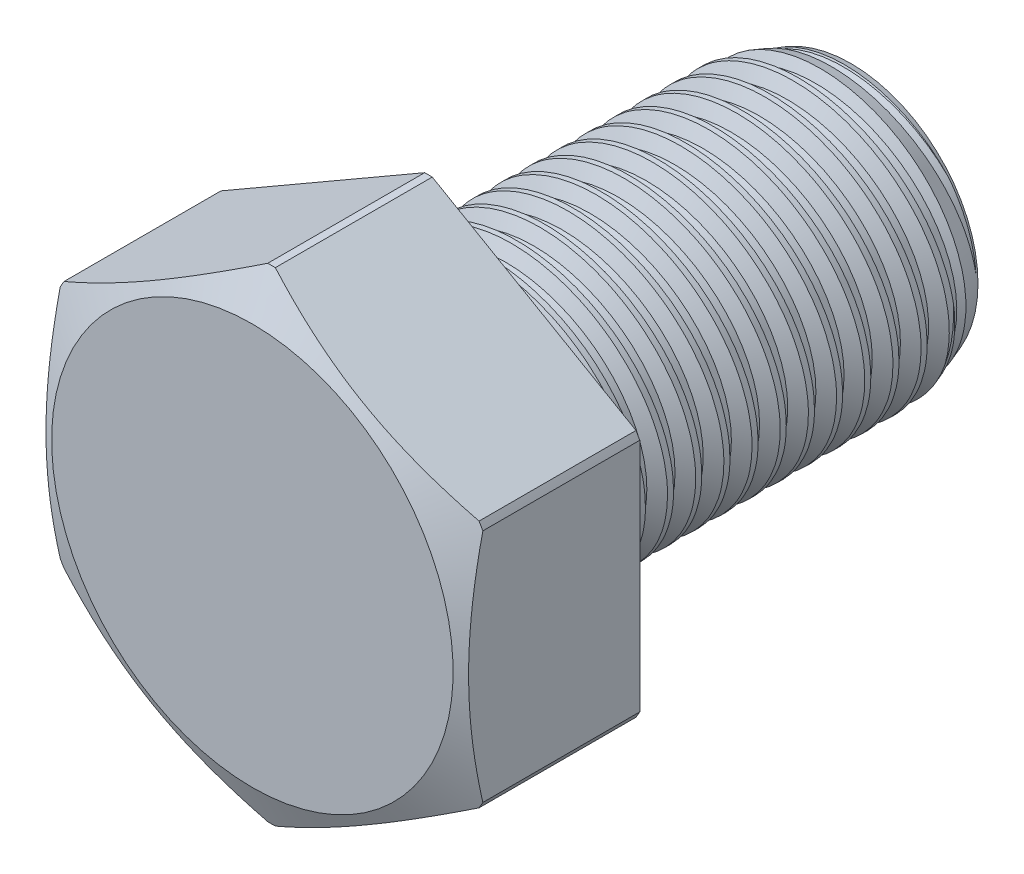
SolidWorks part; units mm, degrees
ref_plane "Front" through (0, 0, 0) normal (0, 0, 1) x (1, 0, 0)
ref_plane "Top" through (0, 0, 0) normal (0, 1, 0) x (1, 0, 0)
ref_plane "Right" through (0, 0, 0) normal (1, 0, 0) x (0, 0, -1)
sketch "Sketch1" plane through (0, 0, 0) normal (1, 0, 0) x (0, 0, -1)
  line L0 (0, 0) -> (-7.9375, 0) construction
  line L1 (0, 0) -> (19.05, 0)
  line L2 (0, 0) -> (0, 6.35)
  line L3 (0, 6.35) -> (19.05, 6.35)
  line L4 (19.05, 0) -> (19.05, 6.35)
  line L5 (0, -6.35) -> (19.05, -6.35) construction
  dimension "D1" = 19.05
  dimension "Thread Dia" = 12.7
  dimension "Length" = 19.05
  dimension "Head Height" = 7.9375
revolve "Revolve1" add sketch "Sketch1" angle 360 about L0
ref_plane "Plane1" through (0, 0, 7.9375) normal (0, 0, 1) x (1, 0, 0)
sketch "Sketch2" plane through (0, 0, 0) normal (1, 0, 0) x (0, 0, -1)
  line L0 (0, 6.35) -> (0, -6.35) construction
  line L1 (0, -6.35) -> (1.27, -6.35) construction
  line L2 (1.27, -6.35) -> (0, 6.35) construction
  line L3 (0, 6.35) -> (0.158, 6.3658) construction
  line L4 (0.158, 6.3658) -> (1.2637, 6.4764)
  line L5 (1.2637, 6.4764) -> (0.9372, 5.7529)
  line L6 (0.9372, 5.7529) -> (0.6213, 5.7213)
  line L7 (0.6213, 5.7213) -> (0.158, 6.3658)
  line L8 (0.7792, 5.7371) -> (0.7108, 6.4211) construction
  line L9 (0, -6.35) -> (19.05, -6.35) construction
  line L10 (0, 6.35) -> (19.05, 6.35) construction
  line L12 (0.7179, 6.35) -> (1.9879, -6.35) construction
  line L13 (0, -0.1353) -> (2.7059, 0.1353) construction
  line L15 (0, 0) -> (0, 6.35) construction
  point P19 (1.3529, 0)
  dimension "D1" = 60
  dimension "Thread Pitch" = 1.27
  dimension "D2" = 0.1588
  dimension "D3" = 0.3175
  dimension "D4" = 1.27
revolve "Cut-Revolve1" cut sketch "Sketch2" angle 360 about L13
sketch "Sketch3" plane through (0, 0, 0) normal (1, 0, 0) x (0, 0, -1)
  line L0 (19.05, 5.7213) -> (17.3226, 6.35)
  line L1 (17.3226, 6.35) -> (19.05, 6.35)
  line L2 (19.05, 6.35) -> (19.05, 5.7213)
  line L3 (0, 6.35) -> (19.05, 6.35) construction
  line L4 (19.05, 0) -> (19.05, 6.35) construction
  line L5 (17.3226, 0) -> (0, 0) construction
  line L6 (17.3226, 6.35) -> (17.3226, -6.35) construction
  line L7 (0, -6.35) -> (19.05, -6.35) construction
  dimension "D1" = 20
  dimension "D2" = 12.7
revolve "Cut-Revolve2" cut sketch "Sketch3" angle 360 about L5
pattern_linear "LPattern1" count 15 spacing 1.27 along (0, 0, 1)
pattern_linear "LPattern2" count 2 spacing 1.27 along (0, 0, 1)
sketch "Sketch4" plane through (0, 0, 0) normal (0, 0, 1) x (1, 0, 0)
  line L1 (0, 10.9985) -> (-9.525, 5.4993)
  line L2 (-9.525, 5.4993) -> (-9.525, -5.4993)
  line L3 (-9.525, -5.4993) -> (0, -10.9985)
  line L4 (0, -10.9985) -> (9.525, -5.4993)
  line L5 (9.525, -5.4993) -> (9.525, 5.4993)
  line L6 (9.525, 5.4993) -> (0, 10.9985)
  circle A0 centre (0, 0) radius 9.525 construction
  circle A1 centre (0, 0) radius 9.525 construction
  dimension "Head Dia" = 19.05
extrude "Extrude1" add sketch "Sketch4" along normal up to surface (7.9375 mm away)
sketch "Sketch9" plane through (0, 0, 0) normal (1, 0, 0) x (0, 0, -1)
  line L0 (-7.9375, 9.0487) -> (-7.0738, 10.901)
  line L1 (0, 10.9985) -> (-7.9375, 10.9985)
  line L2 (-7.9375, 10.9985) -> (-7.9375, 9.0487)
  line L3 (0, 0) -> (-7.9375, 0) construction
  line L4 (-7.9375, 10.9985) -> (0, 10.9985) construction
  line L5 (-7.9375, 5.4993) -> (-7.9375, 10.9985) construction
  line L6 (-7.0738, 10.901) -> (0, 10.901)
  line L10 (0, 10.901) -> (0, 10.9985)
  line L11 (0, 5.4993) -> (0, 10.9985) construction
  dimension "D2" = 18.0975
  dimension "D4" = 0.0975
  dimension "D1" = 25
  dimension "D3" = 1.9498
revolve "Cut-Revolve3" cut sketch "Sketch9" angle 360 about L3
equation "\"D2@Sketch2\"=\"Thread Pitch@Sketch2\"/8"
equation "\"D3@Sketch2\"=\"Thread Pitch@Sketch2\"/4"
equation "\"D4@Sketch2\"=\"Thread Pitch@Sketch2\""
equation "\"D3@LPattern1\"=\"Thread Pitch@Sketch2\""
equation "\"D1@LPattern1\"=\"D1@Sketch1\"/\"Thread Pitch@Sketch2\""
equation "\"D3@LPattern2\"=\"Thread Pitch@Sketch2\""
equation "\"D2@Sketch9\"=\"Head Dia@Sketch4\"*.95"
equation "\"D4@Sketch9\"=\"D3@Sketch9\"/20"
